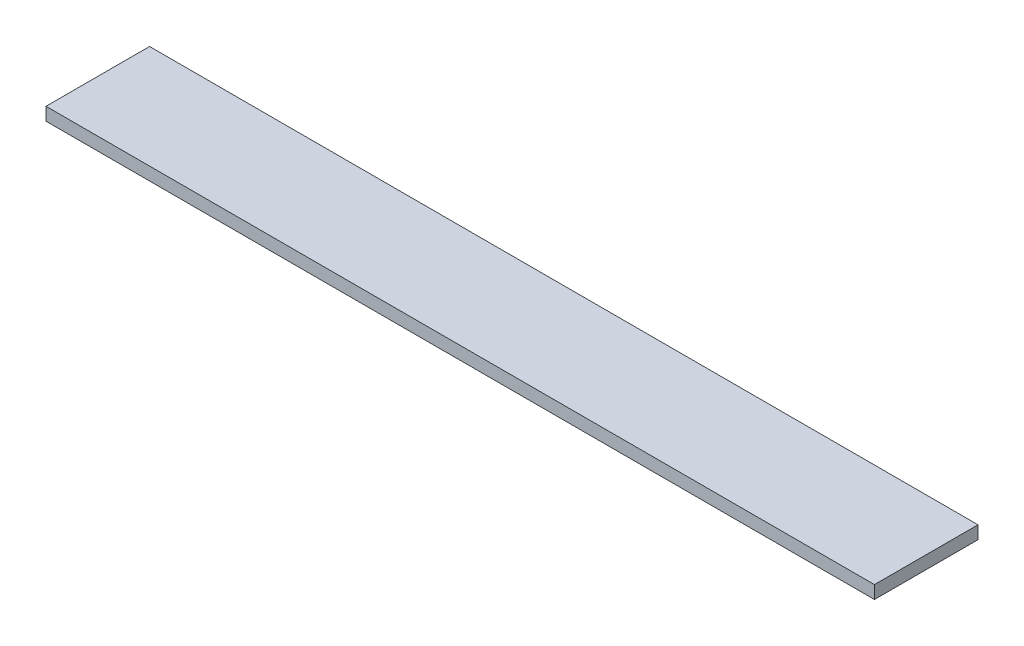
SolidWorks part; units mm, degrees
ref_plane "Front Plane" through (0, 0, 0) normal (0, 0, 1) x (1, 0, 0)
ref_plane "Top Plane" through (0, 0, 0) normal (0, 1, 0) x (1, 0, 0)
ref_plane "Right Plane" through (0, 0, 0) normal (1, 0, 0) x (0, 0, -1)
sketch "Sketch1" plane through (0, 0, 0) normal (0, 1, 0) x (1, 0, 0)
  line L1 (0, 0) -> (609.6, 0)
  line L2 (0, 0) -> (0, 76.2)
  line L3 (0, 76.2) -> (609.6, 76.2)
  line L4 (609.6, 0) -> (609.6, 76.2)
  dimension "D1" = 609.6
  dimension "D2" = 76.2
extrude "Boss-Extrude1" add sketch "Sketch1" along normal blind 9.525
